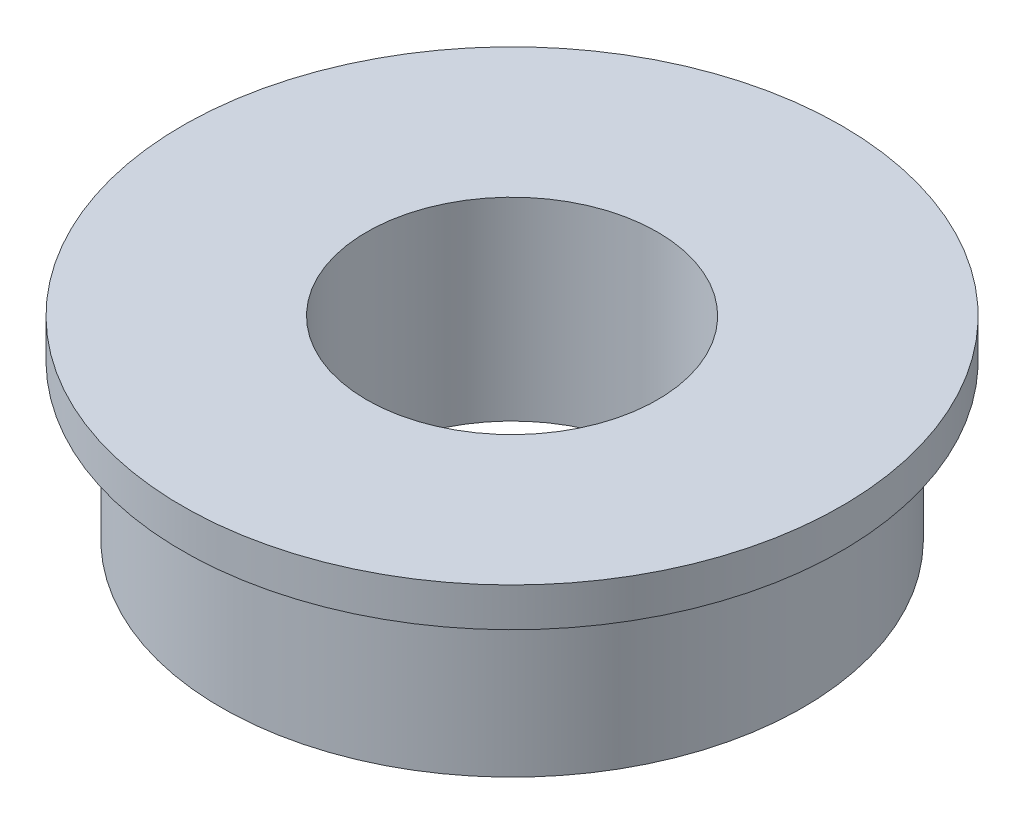
SolidWorks part; units mm, degrees
ref_plane "Plan de face" through (0, 0, 0) normal (0, 0, 1) x (1, 0, 0)
ref_plane "Plan de dessus" through (0, 0, 0) normal (0, 1, 0) x (1, 0, 0)
ref_plane "Plan de droite" through (0, 0, 0) normal (1, 0, 0) x (0, 0, -1)
sketch "Esquisse1" plane through (0, 0, 0) normal (0, 0, 1) x (1, 0, 0)
  line L0 (0, 0) -> (0, 32.6023) construction
  line L2 (3, 4) -> (6.8, 4)
  line L3 (6.8, 4) -> (6.8, 3.2)
  line L4 (3, 0) -> (6, 0)
  line L5 (6, 0) -> (6, 3.2)
  line L6 (6, 3.2) -> (6.8, 3.2)
  line L7 (3, 0) -> (3, 4)
revolve "Révolution1" add sketch "Esquisse1" angle 360 about L0
